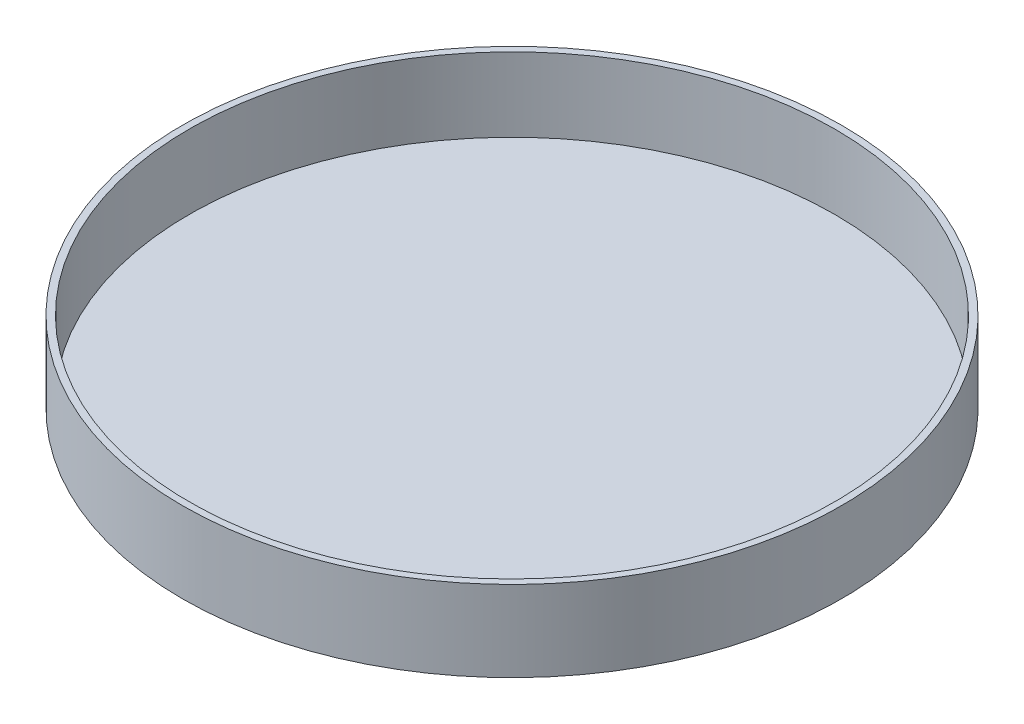
SolidWorks part; units mm, degrees
ref_plane "Front" through (0, 0, 0) normal (0, 0, 1) x (1, 0, 0)
ref_plane "Top" through (0, 0, 0) normal (0, 1, 0) x (1, 0, 0)
ref_plane "Right" through (0, 0, 0) normal (1, 0, 0) x (0, 0, -1)
sketch "Sketch1" plane through (0, 0, 0) normal (1, 0, 0) x (0, 0, -1)
  line L0 (0, 0) -> (-311.15, 0)
  line L1 (-311.15, 0) -> (-311.15, 76.2)
  line L2 (-311.15, 76.2) -> (-304.8, 76.2)
  line L3 (-304.8, 76.2) -> (-304.8, 6.35)
  line L4 (-304.8, 6.35) -> (0, 6.35)
  line L5 (0, 6.35) -> (0, 0)
  line L6 (0, -45.6337) -> (0, 123.0648) construction
  dimension "D1" = 609.6
  dimension "D2" = 6.35
  dimension "D3" = 76.2
  dimension "D4" = 69.85
revolve "Revolve1" add sketch "Sketch1" angle 360 about L6
